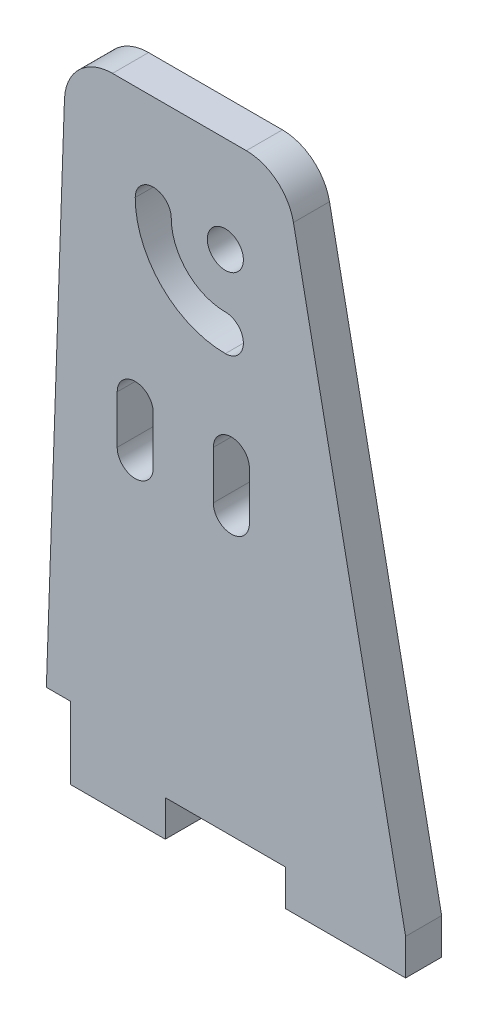
SolidWorks part; units mm, degrees
ref_plane "Front Plane" through (0, 0, 0) normal (0, 0, 1) x (1, 0, 0)
ref_plane "Top Plane" through (0, 0, 0) normal (0, 1, 0) x (1, 0, 0)
ref_plane "Right Plane" through (0, 0, 0) normal (1, 0, 0) x (0, 0, -1)
sketch "Sketch1" plane through (0, 0, 0) normal (0, 0, 1) x (1, 0, 0)
  line L0 (-36.4486, -26.1682) -> (-36.4486, -23.1682)
  line L1 (-36.4486, -26.1682) -> (-26.4486, -26.1682)
  line L2 (-26.4486, -26.1682) -> (-26.4486, -23.1682)
  line L3 (-26.4486, -23.1682) -> (-16.4486, -23.1682)
  line L4 (-16.4486, -23.1682) -> (-16.4486, -26.1682)
  line L5 (-16.4486, -26.1682) -> (-6.4486, -26.1682)
  line L6 (-6.4486, -26.1682) -> (-6.4486, -23.1682)
  line L7 (-6.4486, -23.1682) -> (-15.7798, 23.6142)
  line L8 (-19.7026, 26.8318) -> (-30.8398, 26.8318)
  line L9 (-36.4486, -23.1682) -> (-34.8374, 22.9714)
  line L10 (-28.9486, 4.0743) -> (-28.9486, 0.0743) construction
  line L11 (-27.4486, 4.0743) -> (-27.4486, 0.0743)
  line L12 (-30.4486, 4.0743) -> (-30.4486, 0.0743)
  line L13 (-20.9486, 4.0743) -> (-20.9486, 0.0743) construction
  line L14 (-19.4486, 4.0743) -> (-19.4486, 0.0743)
  line L15 (-22.4486, 4.0743) -> (-22.4486, 0.0743)
  arc A0 (-27.4486, 18.8318) -> (-21.4486, 12.8318) centre (-21.4486, 18.8318) ccw construction
  arc A1 (-28.9486, 18.8318) -> (-21.4486, 11.3318) centre (-21.4486, 18.8318) ccw
  arc A2 (-25.9486, 18.8318) -> (-21.4486, 14.3318) centre (-21.4486, 18.8318) ccw
  arc A3 (-25.9486, 18.8318) -> (-28.9486, 18.8318) centre (-27.4486, 18.8318) ccw
  arc A4 (-21.4486, 11.3318) -> (-21.4486, 14.3318) centre (-21.4486, 12.8318) ccw
  circle A5 centre (-21.4486, 18.8318) radius 1.5
  arc A6 (-15.7798, 23.6142) -> (-19.7026, 26.8318) centre (-19.7026, 22.8318) ccw
  arc A7 (-34.8374, 22.9714) -> (-30.8398, 26.8318) centre (-30.8398, 22.8318) cw
  arc A8 (-27.4486, 4.0743) -> (-30.4486, 4.0743) centre (-28.9486, 4.0743) ccw
  arc A9 (-30.4486, 0.0743) -> (-27.4486, 0.0743) centre (-28.9486, 0.0743) ccw
  arc A10 (-19.4486, 4.0743) -> (-22.4486, 4.0743) centre (-20.9486, 4.0743) ccw
  arc A11 (-22.4486, 0.0743) -> (-19.4486, 0.0743) centre (-20.9486, 0.0743) ccw
  point P11 (-25.6912, 14.5891)
  point P20 (-16.4216, 26.8318)
  point P22 (-34.7026, 26.8318)
  point P27 (-28.9486, 2.0743)
  point P36 (-20.9486, 2.0743)
  dimension "D4" = 1.5
  dimension "D5" = 3
  dimension "D7" = 3
  dimension "D12" = 4
  dimension "D9" = 4
  dimension "D13" = 1.5
  dimension "D1" = 10
  dimension "D2" = 10
  dimension "D3" = 10
  dimension "D6" = 6
  dimension "D8" = 15
  dimension "D10" = 8
  dimension "D11" = 50
  dimension "D14" = 4
  dimension "D15" = 2
extrude "Boss-Extrude1" add sketch "Sketch1" along normal blind 3
sketch "Sketch2" plane through (0, 0, 3) normal (0, 0, 1) x (1, 0, 0)
  line L0 (-34.3438, -26.1682) -> (-34.3438, -20.1682)
  line L1 (-36.4486, -26.1682) -> (-26.4486, -26.1682) construction
  line L2 (-34.3438, -20.1682) -> (-36.3438, -20.1682)
  line L3 (-34.8374, 22.9714) -> (-36.4486, -23.1682) construction
  line L4 (-36.3438, -20.1682) -> (-36.4486, -23.1682)
  line L5 (-36.4486, -23.1682) -> (-36.4486, -26.1682)
  line L6 (-36.4486, -26.1682) -> (-34.3438, -26.1682)
  dimension "D1" = 6
  dimension "D2" = 2
extrude "Cut-Extrude1" cut sketch "Sketch2" against normal through all
